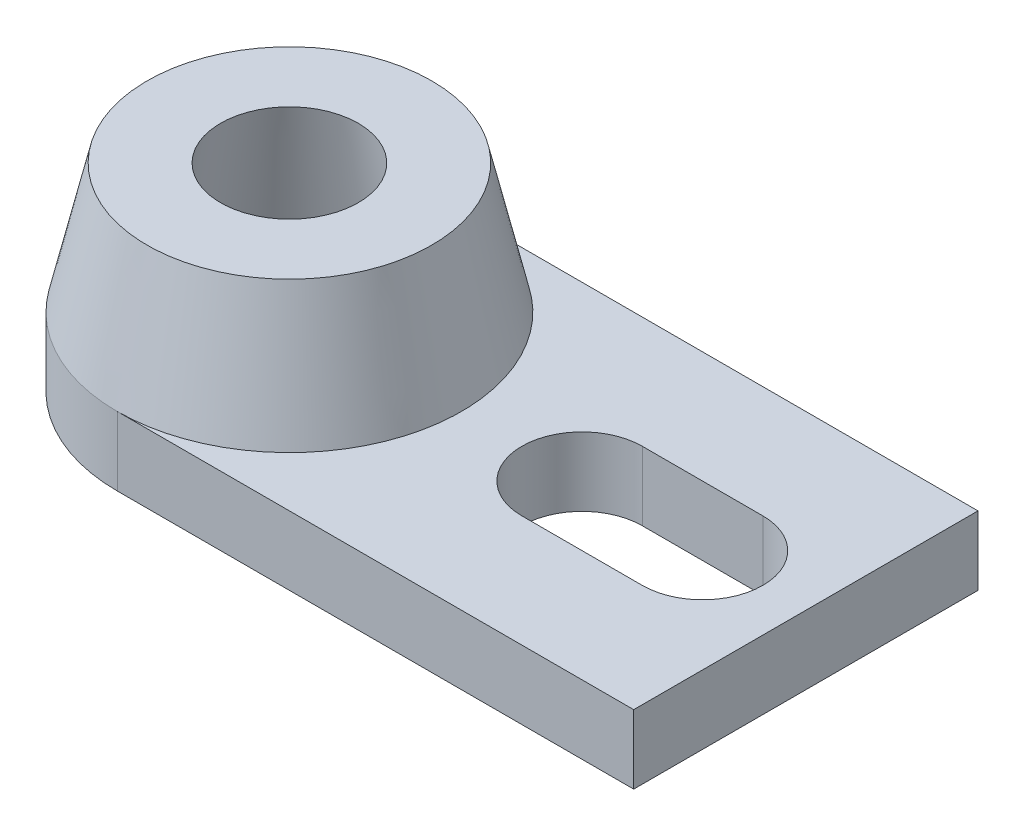
SolidWorks part; units mm, degrees
ref_plane "Alzado" through (0, 0, 0) normal (0, 0, 1) x (1, 0, 0)
ref_plane "Planta" through (0, 0, 0) normal (0, 1, 0) x (1, 0, 0)
ref_plane "Vista lateral" through (0, 0, 0) normal (1, 0, 0) x (0, 0, -1)
sketch "Croquis2" plane through (0, 0, 0) normal (0, 1, 0) x (1, 0, 0)
  line L0 (0, 0) -> (0, 40)
  line L1 (0, 40) -> (-60, 40)
  line L2 (-60, 0) -> (0, 0)
  line L3 (-26, 20) -> (-12, 20) construction
  line L4 (-26, 27) -> (-12, 27)
  line L5 (-26, 13) -> (-12, 13)
  arc A0 (-60, 40) -> (-60, 0) centre (-60, 20) cw
  arc A1 (-26, 27) -> (-26, 13) centre (-26, 20) ccw
  arc A2 (-12, 13) -> (-12, 27) centre (-12, 20) ccw
  point P8 (-19, 20)
  dimension "D5" = 7
  dimension "D1" = 40
  dimension "D2" = 60
  dimension "D3" = 14
  dimension "D4" = 12
extrude "Saliente-Extruir1" add sketch "Croquis2" along normal blind 8
ref_plane "Plano1" through (0, 0, -20) normal (0, 0, 1) x (1, 0, 0)
sketch "Croquis6" plane through (0, 0, -20) normal (0, 0, 1) x (1, 0, 0)
  line L0 (-60, -24.6383) -> (-60, 30.5248) construction
  line L1 (-60, 8) -> (0, 8) construction
  line L2 (-60, 8) -> (-60, 0) construction
  line L3 (-72.0555, 0) -> (-68, 23)
  line L4 (-68, 23) -> (-76.537, 23)
  line L5 (-76.537, 23) -> (-80, 8)
  line L6 (-80, 8) -> (-80, 0)
  line L7 (-80, 0) -> (-72.0555, 0)
  line L9 (-60, 0) -> (0, 0) construction
  line L10 (0, 8) -> (0, 0) construction
  point P2 (0, 0)
  point P16 (-64.6465, 23)
  point P17 (-72.5185, 23)
  point P18 (-69.4526, 23)
  dimension "D1" = 15
  dimension "D2" = 80
  dimension "D3" = 10
  dimension "D4" = 13
  dimension "D5" = 8
revolve "Revolución1" add sketch "Croquis6" angle 360 about L0
